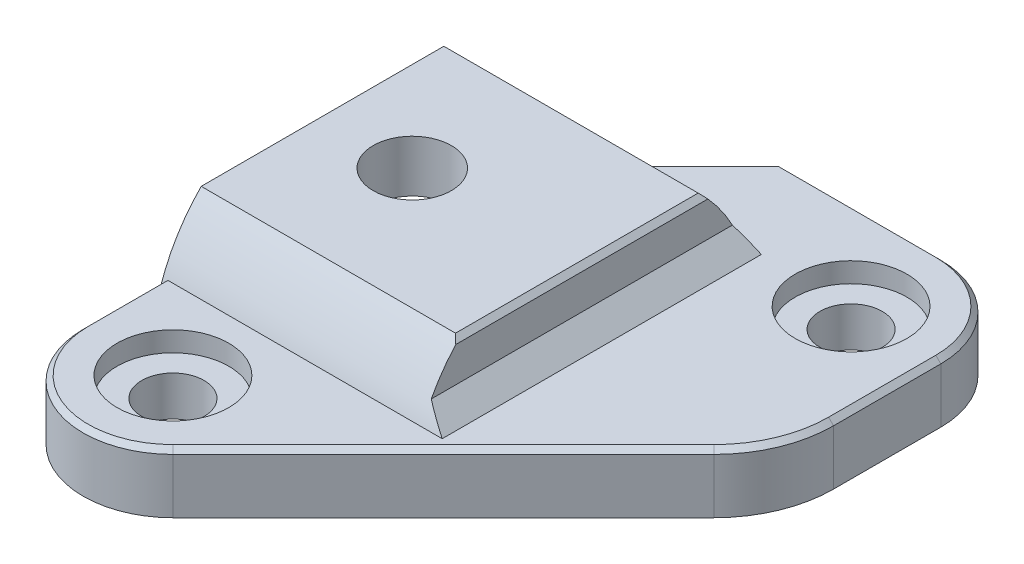
SolidWorks part; units mm, degrees
ref_plane "Front Plane" through (0, 0, 0) normal (0, 0, 1) x (1, 0, 0)
ref_plane "Top Plane" through (0, 0, 0) normal (0, 1, 0) x (1, 0, 0)
ref_plane "Right Plane" through (0, 0, 0) normal (1, 0, 0) x (0, 0, -1)
sketch "Sketch1" plane through (0, 0, 0) normal (0, 1, 0) x (1, 0, 0)
  line L0 (1, 6.5) -> (1, 7.5) construction
  line L1 (3.182, -15.182) -> (18.5, 0.136)
  line L2 (-4.5, -12) -> (-4.5, -6.5)
  line L3 (6, 12.5) -> (14, 12.5)
  line L4 (18.5, 0.136) -> (18.5, 8)
  line L5 (-4.5, -6.5) -> (8, -6.5) construction
  line L6 (8, 0) -> (0, 0) construction
  line L7 (1, 6.5) -> (8, 6.5) construction
  line L8 (8, -6.5) -> (8, 6.5) construction
  line L9 (1, 7.5) -> (6, 12.5)
  line L10 (-4.5, -6.5) -> (-4.5, 2)
  line L11 (-4.5, 2) -> (1, 7.5)
  circle A0 centre (0, -12) radius 1.5625
  circle A1 centre (14, 8) radius 1.5625
  arc A2 (18.5, 8) -> (14, 12.5) centre (14, 8) ccw
  arc A3 (3.182, -15.182) -> (-4.5, -12) centre (0, -12) cw
  dimension "D1" = 3.125
  dimension "D2" = 13
  dimension "D3" = 1
  dimension "D4" = 8
  dimension "D5" = 12.5
  dimension "D6" = 45
  dimension "D7" = 45
  dimension "D8" = 1
  dimension "D9" = 12
  dimension "D10" = 14
  dimension "D11" = 8
extrude "Boss-Extrude1" add sketch "Sketch1" along normal blind 3
sketch "Sketch2" plane through (-4.5, 0, 0) normal (-1, 0, 0) x (0, 0, 1)
  line L1 (-8, 0) -> (8, 0)
  line L2 (-8, 0) -> (-8, 3)
  line L3 (-6.0828, 6) -> (6.0828, 6)
  line L4 (8, 0) -> (8, 3)
  line L5 (-2, 3) -> (12, 3) construction
  arc A0 (-8, 3) -> (-6.0828, 6) centre (0, 0) cw
  arc A1 (6.0828, 6) -> (8, 3) centre (0, 0) cw
  dimension "D1" = 16
  dimension "D2" = 6
extrude "Boss-Extrude2" add sketch "Sketch2" against normal blind 13
sketch "Sketch3" plane through (-4.5, 0, 0) normal (-1, 0, 0) x (0, 0, 1)
  line L0 (-8, 0) -> (12, 0) construction
  line L1 (-6.75, 0) -> (6.75, 0)
  line L2 (-5.8312, 3.4) -> (5.8312, 3.4)
  arc A0 (-6.75, 0) -> (-5.8312, 3.4) centre (0, 0) cw
  arc A1 (5.8312, 3.4) -> (6.75, 0) centre (0, 0) cw
  dimension "D1" = 13.5
  dimension "D2" = 3.4
extrude "Cut-Extrude1" cut sketch "Sketch3" against normal blind 11.5
sketch "Sketch4" plane through (0, 6, 0) normal (0, 1, 0) x (1, 0, 0)
  circle A0 centre (0, 0) radius 1.96
  dimension "D1" = 3.92
extrude "Cut-Extrude2" cut sketch "Sketch4" against normal through all
chamfer "Chamfer1" distance 1 angle 45 1 edges at (8.5, 3, 0)
fillet "Fillet1" radius 6 1 edges at (18.5, 1.5, -0.136)
chamfer "Chamfer2" distance 3.4 angle 45 1 edges at (-4.5, 0, -7.375)
chamfer "Chamfer3" distance 0.5 angle 45 3 edges at (7, 1.761, 6.5162) (7, 3.4, 0) (7, 1.761, -6.5162)
sketch "Sketch5" plane through (0, 3, 0) normal (0, 1, 0) x (1, 0, 0)
  circle A0 centre (0, -12) radius 2.8
  circle A1 centre (14, 8) radius 2.8
  circle A2 centre (14, 8) radius 1.5625 construction
  circle A3 centre (0, -12) radius 1.5625 construction
  dimension "D1" = 5.6
extrude "Cut-Extrude3" cut sketch "Sketch5" against normal blind 1
sketch "Sketch6" plane through (0, 0, 0) normal (0, -1, 0) x (1, 0, 0)
  circle A0 centre (4.5, 9.75) radius 1.25
  circle A1 centre (11.5, 0) radius 2
  circle A2 centre (7.5, -9.5) radius 1.25
  dimension "D1" = 2.5
  dimension "D2" = 4
  dimension "D3" = 11.5
  dimension "D4" = 9.5
  dimension "D5" = 9.75
  dimension "D6" = 7.5
  dimension "D7" = 4.5
extrude "Boss-Extrude3" add sketch "Sketch6" along normal blind 1
chamfer "Chamfer4" distance 0.25 angle 45 12 edges at (8.5, 6, 0) (3.75, 3, -10.25) (10, 3, -12.5) (17.182, 3, -11.182) (-4.5, 3, 10) (18.5, 3, -5.3107) (-1.7221, 3, 16.1575) (18.0433, 3, -0.3252) (9.9623, 3, 8.4017) (4.5, -1, 8.5) (11.5, -1, -2) (7.5, -1, -10.75)
